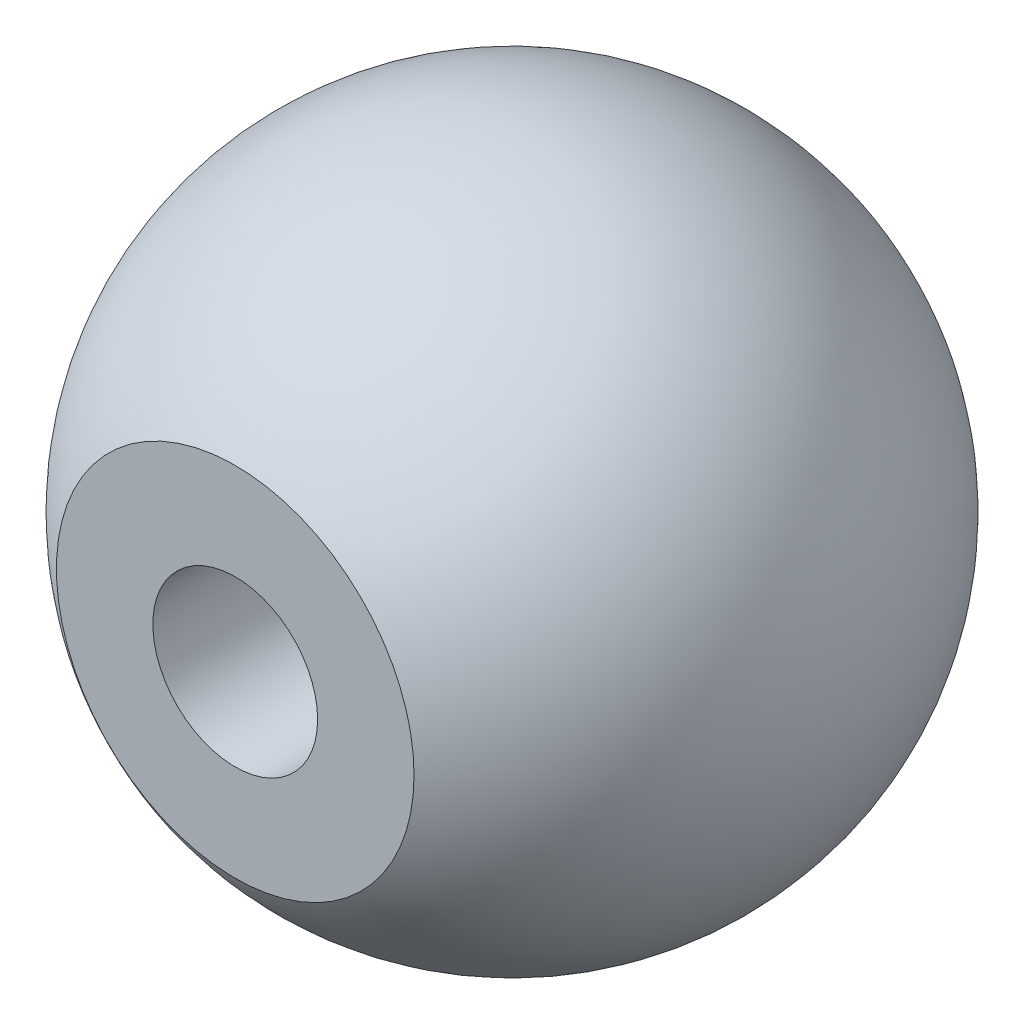
SolidWorks part; units mm, degrees
ref_plane "Front Plane" through (0, 0, 0) normal (0, 0, 1) x (1, 0, 0)
ref_plane "Top Plane" through (0, 0, 0) normal (0, 1, 0) x (1, 0, 0)
ref_plane "Right Plane" through (0, 0, 0) normal (1, 0, 0) x (0, 0, -1)
sketch "Sketch1" plane through (0, 0, 0) normal (0, 1, 0) x (1, 0, 0)
  line L0 (-19.05, 0) -> (0, 0) construction
  line L1 (0, 0) -> (19.05, 0)
  line L2 (0, 0) -> (-19.05, 0)
  arc A0 (-19.05, 0) -> (19.05, 0) centre (0, 0) ccw
  dimension "D1" = 38.1
revolve "Revolve6" add sketch "Sketch1" angle 360 about L0
ref_plane "Plane1" through (0, 0, 16.002) normal (0, 0, 1) x (1, 0, 0)
sketch "Sketch3" plane through (0, 0, 16.002) normal (0, 0, 1) x (1, 0, 0)
  line L1 (-18.5128, 14.6768) -> (18.5128, 14.6768)
  line L2 (-18.5128, 14.6768) -> (-18.5128, -14.6768)
  line L3 (-18.5128, -14.6768) -> (18.5128, -14.6768)
  line L4 (18.5128, 14.6768) -> (18.5128, -14.6768)
  line L5 (-18.5128, 14.6768) -> (18.5128, -14.6768) construction
  line L6 (-18.5128, -14.6768) -> (18.5128, 14.6768) construction
  point P0 (0, 0)
  dimension "D1" = 29.3537
  dimension "D2" = 37.0256
extrude "Cut-Extrude1" cut sketch "Sketch3" along normal blind 3.048
sketch "Sketch4" plane through (0, 0, 16.002) normal (0, 0, 1) x (1, 0, 0)
  circle A0 centre (0, 0) radius 4.7625
  dimension "D1" = 9.525
extrude "Cut-Extrude2" cut sketch "Sketch4" against normal blind 12.7
